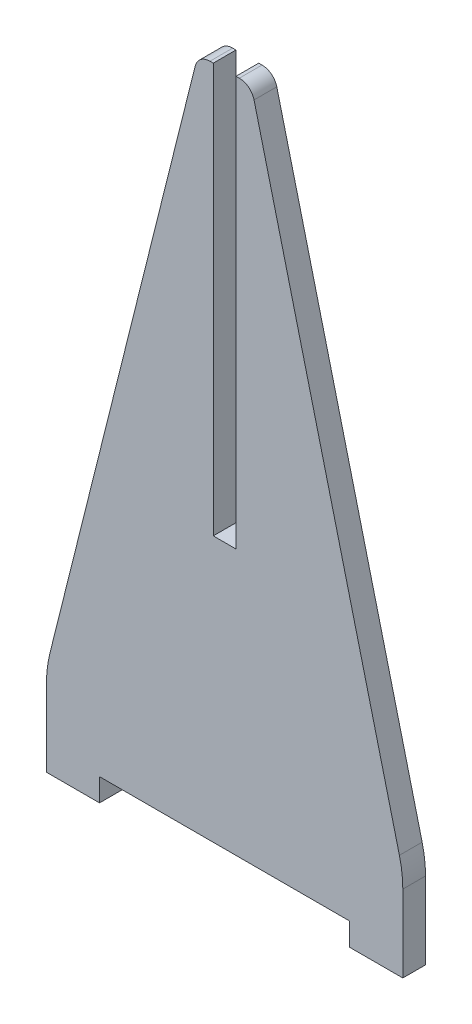
SolidWorks part; units mm, degrees
ref_plane "Plano frontal" through (0, 0, 0) normal (0, 0, 1) x (1, 0, 0)
ref_plane "Plano superior" through (0, 0, 0) normal (0, 1, 0) x (1, 0, 0)
ref_plane "Plano direito" through (0, 0, 0) normal (1, 0, 0) x (0, 0, -1)
sketch "Esboço1" plane through (0, 0, 0) normal (0, 0, 1) x (1, 0, 0)
  line L0 (-23.5, 0) -> (23.5, 0) construction
  line L1 (-23.5, 0) -> (-16.5, 0)
  line L2 (-16.5, 0) -> (-16.5, 3)
  line L3 (23.5, 0) -> (16.5, 0)
  line L4 (16.5, 0) -> (16.5, 3)
  line L5 (-16.5, 3) -> (16.5, 3)
  line L6 (-23.5, 0) -> (-23.5, 12)
  line L7 (23.5, 0) -> (23.5, 12)
  line L8 (-23.5, 12) -> (-3.5, 92)
  line L10 (23.5, 12) -> (3.5, 92)
  line L12 (-3.5, 92) -> (-1.5, 92)
  line L13 (1.5, 92) -> (3.5, 92)
  line L14 (-1.5, 38) -> (1.5, 38)
  line L15 (-1.5, 38) -> (-1.5, 92)
  line L17 (1.5, 38) -> (1.5, 92)
  line L18 (-1.5, 38) -> (1.5, 92) construction
  line L19 (-1.5, 92) -> (1.5, 38) construction
  point P0 (0, 65)
  point P4 (0, 0)
  dimension "D4" = 3
  dimension "D8" = 7
  dimension "D1" = 47
  dimension "D2" = 3
  dimension "D3" = 7
  dimension "D5" = 12
  dimension "D6" = 35
  dimension "D7" = 80
extrude "Ressalto-extrusão1" add sketch "Esboço1" along normal blind 3
fillet "Filete1" radius 15 2 edges at (23.5, 12, 1.5) (-23.5, 12, 1.5)
fillet "Filete2" radius 2 2 edges at (-3.5, 92, 1.5) (3.5, 92, 1.5)
